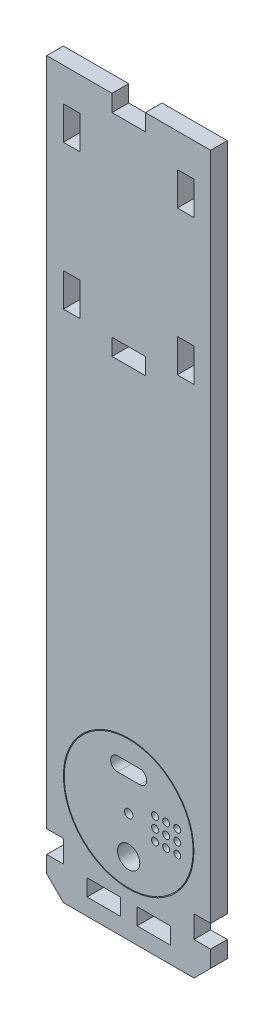
SolidWorks part; units mm, degrees
ref_plane "Front Plane" through (0, 0, 0) normal (0, 0, 1) x (1, 0, 0)
ref_plane "Top Plane" through (0, 0, 0) normal (0, 1, 0) x (1, 0, 0)
ref_plane "Right Plane" through (0, 0, 0) normal (1, 0, 0) x (0, 0, -1)
sketch "Sketch2" plane through (0, 0, 0) normal (0, 1, 0) x (1, 0, 0)
  line L0 (0, 0) -> (0, 6) construction
  dimension "D1" = 6
sketch "Sketch1" plane through (0, 0, 0) normal (0, 0, 1) x (1, 0, 0)
  line L0 (0, 33.5) -> (0, 20) construction
  line L1 (-29.5, 0) -> (29.5, 0)
  line L2 (-29.5, 0) -> (-29.5, 255)
  line L3 (-29.5, 255) -> (29.5, 255)
  line L4 (29.5, 0) -> (29.5, 255)
  line L5 (0, 10) -> (0, 16) construction
  line L6 (0, 10) -> (0, 6) construction
  line L7 (-23.5, 33.5) -> (-29.5, 33.5) construction
  line L8 (-29.5, 179) -> (29.5, 179) construction
  line L9 (-23.5, 173) -> (-23.5, 249) construction
  line L10 (-29.5, 249) -> (29.5, 249) construction
  line L11 (29.5, 6) -> (-29.5, 6) construction
  line L12 (0, 6) -> (0, 0) construction
  line L13 (0, 179) -> (0, 173) construction
  line L14 (0, 249) -> (0, 255) construction
  line L15 (-29.5, 239) -> (29.5, 239) construction
  line L16 (23.5, 173) -> (23.5, 249) construction
  line L21 (-21, 173) -> (21, 173) construction
  line L22 (0, 33.5) -> (13.5, 33.5) construction
  line L24 (9.5, 29.5) -> (17.5, 29.5) construction
  line L25 (9.5, 29.5) -> (9.5, 37.5) construction
  line L26 (9.5, 37.5) -> (17.5, 37.5) construction
  line L27 (17.5, 29.5) -> (17.5, 37.5) construction
  line L28 (9.5, 29.5) -> (17.5, 37.5) construction
  line L29 (9.5, 37.5) -> (17.5, 29.5) construction
  line L30 (0, 33.5) -> (0, 47) construction
  line L31 (-4, 47) -> (4, 47) construction
  line L32 (-4, 49.5) -> (4, 49.5)
  line L33 (-4, 44.5) -> (4, 44.5)
  line L34 (-21, 173) -> (-23.5, 173) construction
  line L35 (21, 173) -> (23.5, 173) construction
  line L36 (21, 173) -> (21, 6) construction
  line L37 (21, 6) -> (23.5, 6) construction
  line L38 (23.5, 6) -> (23.5, 173) construction
  line L39 (-23.5, 173) -> (-23.5, 6) construction
  line L40 (-21, 173) -> (-21, 6) construction
  circle A0 centre (0, 33.5) radius 23.5
  circle A1 centre (0, 20) radius 4
  circle A2 centre (0, 33.5) radius 23.2
  circle A5 centre (9.5, 29.5) radius 1.25
  circle A6 centre (13.5, 29.5) radius 1.25
  circle A7 centre (17.5, 29.5) radius 1.25
  circle A8 centre (13.5, 33.5) radius 1.25
  circle A9 centre (17.5, 33.5) radius 1.25
  circle A10 centre (17.5, 37.5) radius 1.25
  circle A11 centre (13.5, 37.5) radius 1.25
  circle A12 centre (9.5, 37.5) radius 1.25
  circle A13 centre (9.5, 33.5) radius 1.25
  arc A14 (-4, 49.5) -> (-4, 44.5) centre (-4, 47) ccw
  arc A15 (4, 44.5) -> (4, 49.5) centre (4, 47) ccw
  circle A16 centre (0, 33.5) radius 1.5
  point P35 (0, 173)
  point P57 (0, 47)
  dimension "D4" = 8
  dimension "D13" = 2.5
  dimension "D18" = 3
  dimension "D1" = 59
  dimension "D2" = 255
  dimension "D3" = 6
  dimension "D5" = 20
  dimension "D6" = 6
  dimension "D7" = 0.3
  dimension "D8" = 6
  dimension "D10" = 60
  dimension "D11" = 10
  dimension "D12" = 8
  dimension "D14" = 8
  dimension "D15" = 5
  dimension "D16" = 42
  dimension "D17" = 2.5
  dimension "D9" = 167
extrude "Boss-Extrude1" add sketch "Sketch1" against normal up to vertex (6 mm away) contours L1 L4 L3 L2 A0 | A2 A15 L33 A14 L32 A13 A12 A11 A10 A9 A8 A7 A6 A5 A1
sketch "Sketch3" plane through (0, 0, 0) normal (0, 0, 1) x (1, 0, 0)
  line L0 (0, 249) -> (0, 255) construction
  line L1 (-6, 249) -> (6, 249)
  line L2 (-6, 249) -> (-6, 255)
  line L3 (-6, 255) -> (6, 255)
  line L4 (6, 249) -> (6, 255)
  line L5 (-6, 249) -> (6, 255) construction
  line L6 (-6, 255) -> (6, 249) construction
  line L7 (-29.5, 255) -> (29.5, 255) construction
  line L8 (-6, 249) -> (-29.5, 249)
  line L9 (6, 249) -> (29.5, 249)
  line L10 (0, 179) -> (0, 173) construction
  line L11 (-6, 173) -> (6, 173)
  line L12 (-6, 173) -> (-6, 179)
  line L13 (-6, 179) -> (6, 179)
  line L14 (6, 173) -> (6, 179)
  line L15 (-6, 173) -> (6, 179) construction
  line L16 (-6, 179) -> (6, 173) construction
  line L17 (-29.5, 179) -> (29.5, 179) construction
  line L18 (-23.5, 173) -> (-23.5, 249) construction
  line L19 (-23.5, 191) -> (-17.5, 191)
  line L20 (-23.5, 191) -> (-23.5, 179)
  line L21 (-23.5, 179) -> (-17.5, 179)
  line L22 (-17.5, 191) -> (-17.5, 179)
  line L23 (23.5, 173) -> (23.5, 249) construction
  line L24 (23.5, 191) -> (17.5, 191)
  line L25 (23.5, 191) -> (23.5, 179)
  line L26 (23.5, 179) -> (17.5, 179)
  line L27 (17.5, 191) -> (17.5, 179)
  line L28 (-17.5, 243) -> (-17.5, 249) construction
  line L29 (-23.5, 243) -> (-17.5, 243)
  line L30 (-23.5, 243) -> (-23.5, 231)
  line L31 (-23.5, 231) -> (-17.5, 231)
  line L32 (-17.5, 243) -> (-17.5, 231)
  line L33 (23.5, 243) -> (17.5, 243)
  line L34 (23.5, 243) -> (23.5, 231)
  line L35 (23.5, 231) -> (17.5, 231)
  line L36 (17.5, 243) -> (17.5, 231)
  line L37 (0, 6) -> (0, 0) construction
  line L38 (-3, 0) -> (3, 0)
  line L39 (-3, 0) -> (-3, 6)
  line L40 (-3, 6) -> (3, 6)
  line L41 (3, 0) -> (3, 6)
  line L42 (-3, 0) -> (3, 6) construction
  line L43 (-3, 6) -> (3, 0) construction
  line L44 (29.5, 6) -> (-29.5, 6) construction
  line L45 (-29.5, 0) -> (-29.5, 255) construction
  line L46 (-23.5, 6) -> (-29.5, 6)
  line L47 (-23.5, 6) -> (-23.5, 14)
  line L48 (-23.5, 14) -> (-29.5, 14)
  line L49 (-29.5, 6) -> (-29.5, 14)
  line L50 (29.5, 0) -> (29.5, 255) construction
  line L51 (23.5, 6) -> (29.5, 6)
  line L52 (23.5, 6) -> (23.5, 14)
  line L53 (23.5, 14) -> (29.5, 14)
  line L54 (29.5, 6) -> (29.5, 14)
  line L55 (-29.5, 0) -> (29.5, 0) construction
  line L56 (-3, 6) -> (-15, 6)
  line L57 (-3, 6) -> (-3, 0)
  line L58 (-3, 0) -> (-15, 0)
  line L59 (-15, 6) -> (-15, 0)
  line L61 (3, 6) -> (15, 6)
  line L62 (3, 6) -> (3, 0)
  line L63 (3, 0) -> (15, 0)
  line L64 (15, 6) -> (15, 0)
  point P0 (0, 252)
  point P9 (0, 176)
  point P42 (0, 3)
  dimension "D3" = 6
  dimension "D2" = 12
  dimension "D5" = 8
  dimension "D4" = 6
  dimension "D6" = 12
  dimension "D1" = 12
  dimension "D7" = 12
extrude "Cut-Extrude1" cut sketch "Sketch3" against normal blind 10 contours L49 L46 L47 L48 | L51 L54 L53 L52 | L33 L36 L35 L34 | L24 L27 L26 L25 | L11 L14 L13 L12 | L22 L19 L20 L21 | L32 L29 L30 L31 | L1 L4 L3 L2 | L56 L59 L58 L39 | L64 L61 L41 L63
sketch "Sketch5" plane through (0, 0, 0) normal (0, 0, 1) x (1, 0, 0)
  line L0 (-29.5, 0) -> (-23.5, 0)
  line L1 (-29.5, 0) -> (29.5, 0) construction
  line L2 (-23.5, 0) -> (23.5, 0)
  line L3 (23.5, 0) -> (29.5, 0)
  line L4 (29.5, 0) -> (23.5, -6)
  line L5 (23.5, -6) -> (-23.5, -6)
  line L6 (-23.5, -6) -> (-29.5, 0)
  line L7 (-23.5, -6) -> (-23.5, 0) construction
  line L8 (23.5, 0) -> (23.5, -6) construction
  dimension "D1" = 6
extrude "Boss-Extrude3" add sketch "Sketch5" against normal up to surface (6 mm away) up to face at (-20.5, 237, -6)
equation "\"t_wood\"= 6' Thickness of the wood"
equation "\"t_glass\"= 2.5'Thickness of glass panels"
equation "\"w_glass\"= 248"
equation "\"h_glass\"= 167"
equation "\"h_food_internal\" = 60"
equation "\"entry_height\"= 20"
equation "\"entry diameter\"= 8"
equation "\"glass_bottom_overlap\"= 8"
equation "\"default_finger_size\"= 12"
equation "\"brood_depth\"= 42"
equation "\"outer_box_depth\" = \"brood_depth\" + ( 2 * \"t_glass\" ) + ( 2 * \"t_wood\" )"
equation "\"outer_box_width\"= \"w_glass\" + ( 2 * \"t_wood\" )"
equation "\"food_top_clearance\"= 10"
equation "\"outer_box_height\"= \"t_wood\" + \"h_glass\" + \"t_wood\" + \"h_food_internal\" + \"food_top_clearance\" + \"t_wood\""
equation "\"food_internal_depth\"= \"brood_depth\" + \"t_glass\" + \"t_glass\" - \"t_wood\" - \"t_wood\""
equation "\"food_channel_clearance_width\"= 14"
equation "\"bar_top_play\"= 4.5"
equation "\"bar_entry_angle\"= 10"
equation "\"bar_width\"= 20"
equation "\"entry_disk_play\"= 0.3"
equation "\"D1@Sketch1\"=\"outer_box_depth\""
equation "\"D2@Sketch1\"=\"outer_box_height\""
equation "\"D3@Sketch1\"=\"t_wood\""
equation "\"D4@Sketch1\"=\"entry diameter\""
equation "\"D5@Sketch1\"=\"entry_height\""
equation "\"D6@Sketch1\"=\"t_wood\""
equation "\"D7@Sketch1\"=\"entry_disk_play\""
equation "\"D8@Sketch1\"=\"t_wood\""
equation "\"D10@Sketch1\"=\"h_food_internal\""
equation "\"D12@Sketch1\"=\"entry diameter\""
equation "\"D14@Sketch1\"=\"entry diameter\""
equation "\"D16@Sketch1\"=\"brood_depth\""
equation "\"D17@Sketch1\"=\"t_glass\""
equation "\"D9@Sketch1\"=\"h_glass\""
equation "\"D1@Sketch2\"=\"t_wood\""
equation "\"D2@Sketch3\"=\"default_finger_size\""
equation "\"D3@Sketch3\"=\"t_wood\""
equation "\"D5@Sketch3\"=\"glass_bottom_overlap\""
equation "\"D1@Sketch5\"=\"t_wood\""
equation "\"D4@Sketch3\"=\"t_wood\""
equation "\"D6@Sketch3\"=\"default_finger_size\""
equation "\"D1@Sketch3\"=\"default_finger_size\""
equation "\"D7@Sketch3\"=\"default_finger_size\""
